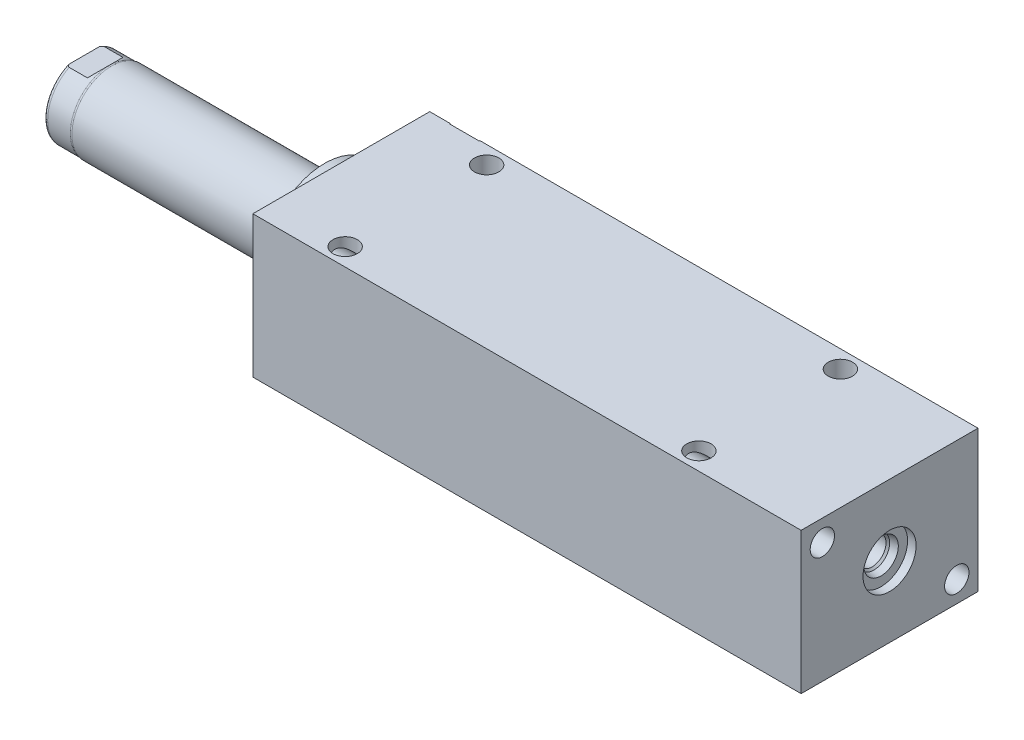
SolidWorks part; units mm, degrees
material "Alloy Steel"
ref_plane "Front Plane" through (0, 0, 0) normal (0, 0, 1) x (1, 0, 0)
ref_plane "Top Plane" through (0, 0, 0) normal (0, 1, 0) x (1, 0, 0)
ref_plane "Right Plane" through (0, 0, 0) normal (1, 0, 0) x (0, 0, -1)
ref_plane "Plane1" through (0, 0, 0) normal (1, 0, 0) x (0, 0, -1)
sketch "Sketch1" plane through (0, 0, 0) normal (1, 0, 0) x (0, 0, -1)
  line L0 (-31.75, 25.4) -> (31.75, 25.4)
  line L1 (31.75, 25.4) -> (31.75, -25.4)
  line L2 (31.75, -25.4) -> (-31.75, -25.4)
  line L3 (-31.75, -25.4) -> (-31.75, 25.4)
  line L4 (0, -24.4475) -> (0, 24.4475) construction
  dimension "D1" = 50.8
  dimension "D2" = 25.4
  dimension "D3" = 63.5
extrude "Extrude1" add sketch "Sketch1" along normal blind 196.85
ref_plane "Plane12" through (0, 17.4752, 0) normal (0, 1, 0) x (-1, 0, 0)
sketch "S2D0002" plane through (0, 17.4752, 0) normal (0, 1, 0) x (-1, 0, 0)
  line L0 (-18.8849, -31.496) -> (-22.225, -31.496)
  line L1 (-18.8849, -31.496) -> (-18.3423, -28.9433)
  line L2 (-18.3423, -28.9433) -> (-17.6784, -28.2794)
  line L3 (-17.6784, -28.2794) -> (-17.6784, -17.526)
  line L4 (-17.6784, -17.526) -> (-12.7, -17.526)
  line L5 (-12.7, -17.526) -> (-12.7, -31.75)
  line L6 (-12.7, -19.1384) -> (-12.7, 0.6985) construction
  line L7 (0, -31.75) -> (0, 31.75) construction
  line L8 (-22.225, -31.75) -> (-22.225, -31.496)
  line L9 (-196.85, -31.75) -> (0, -31.75) construction
  line L10 (-22.225, -31.75) -> (-12.7, -31.75)
  dimension "D1" = 14.224
  dimension "D2" = 12.7
  dimension "D3" = 9.9568
  dimension "D4" = 45
  dimension "D5" = 12.3698
  dimension "D6" = 12
  dimension "D7" = 2.5527
  dimension "D8" = 0.254
  dimension "D9" = 19.05
revolve "Cut-Revolve1" cut sketch "S2D0002" angle 360 about L6
ref_plane "Plane3" through (41.148, 0, -25.146) normal (0, 1, 0) x (1, 0, 0)
sketch "Sketch3" plane through (41.148, 0, -25.146) normal (0, 1, 0) x (1, 0, 0)
  line L0 (146.7993, 6.35) -> (150.1394, 6.35)
  line L1 (146.7993, 6.35) -> (146.2567, 3.7973)
  line L2 (146.2567, 3.7973) -> (145.5928, 3.1334)
  line L3 (145.5928, 3.1334) -> (145.5928, -7.62)
  line L4 (145.5928, -7.62) -> (140.6144, -7.62)
  line L5 (140.6144, -7.62) -> (140.6144, 6.604)
  line L6 (140.6144, -21.9564) -> (140.6144, 0.6985) construction
  line L7 (-41.148, 6.604) -> (-41.148, -56.896) construction
  line L8 (150.1394, 6.604) -> (150.1394, 6.35)
  line L9 (155.702, 6.604) -> (-23.1638, 6.604) construction
  line L10 (150.1394, 6.604) -> (140.6144, 6.604)
  dimension "D1" = 14.224
  dimension "D2" = 181.7624
  dimension "D3" = 9.9568
  dimension "D4" = 45
  dimension "D5" = 12
  dimension "D6" = 12.3698
  dimension "D7" = 2.5527
  dimension "D8" = 0.254
  dimension "D9" = 19.05
revolve "Cut-Revolve2" cut sketch "Sketch3" angle 360 about L6
ref_plane "Plane4" through (53.975, 0, 0) normal (0, 0, 1) x (0, -1, 0)
sketch "Sketch4" plane through (53.975, 0, 0) normal (0, 0, 1) x (0, -1, 0)
  line L0 (6.1849, 139.827) -> (9.525, 139.827)
  line L1 (6.1849, 139.827) -> (5.6423, 137.2743)
  line L2 (5.6423, 137.2743) -> (4.9784, 136.6104)
  line L3 (4.9784, 136.6104) -> (4.9784, 128.4732)
  line L4 (4.9784, 128.4732) -> (0, 128.4732)
  line L5 (0, 128.4732) -> (0, 142.875)
  line L6 (0, -15.0954) -> (0, 0.5677) construction
  line L7 (0, 142.875) -> (9.525, 142.875)
  line L9 (-25.4, 142.875) -> (25.4, 142.875) construction
  line L10 (9.525, 142.875) -> (9.525, 139.827)
  dimension "D1" = 11.3538
  dimension "D2" = 9.9568
  dimension "D3" = 3.048
  dimension "D4" = 19.05
  dimension "D5" = 2.5527
  dimension "D6" = 12
  dimension "D7" = 45
  dimension "D8" = 12.3698
revolve "Cut-Revolve3" cut sketch "Sketch4" angle 360 about L6
sketch "Sketch5" plane through (0, 0, 0) normal (-1, 0, 0) x (0, 0, 1)
  circle A0 centre (0, 0) radius 22.225
  dimension "D1" = 44.45
extrude "Extrude2" add sketch "Sketch5" along normal blind 5.969
ref_plane "Plane5" through (0, 0, 0) normal (0, -1, 0) x (0, 0, 1)
sketch "Sketch6" plane through (0, 0, 0) normal (0, -1, 0) x (0, 0, 1)
  line L0 (0, 5.969) -> (-14.2875, 5.969)
  line L1 (-14.2875, 5.969) -> (-14.2875, 92.329)
  line L2 (-14.2875, 92.329) -> (0, 92.329)
  line L3 (0, 92.329) -> (0, 5.969)
  line L4 (0, -5.7546) -> (0, 21.1709) construction
  line L5 (22.225, 5.969) -> (-22.225, 5.969) construction
  line L6 (31.75, -196.85) -> (-31.75, -196.85) construction
  dimension "D1" = 289.179
  dimension "D2" = 28.575
revolve "Revolve1" add sketch "Sketch6" angle 360 about L4
ref_plane "Plane6" through (-18.5113, 3.2639, 0) normal (0, 0, 1) x (0, 1, 0)
sketch "S2D0001" plane through (-18.5113, 3.2639, 0) normal (0, 0, 1) x (0, 1, 0)
  line L0 (2.286, 71.75) -> (2.286, 57.4347)
  line L1 (2.286, 57.4347) -> (-3.2639, 57.4347)
  line L2 (3.4798, 73.8177) -> (-3.2639, 73.8177)
  line L3 (-3.2639, 73.8177) -> (-3.2639, 57.4347)
  line L4 (2.286, 71.75) -> (3.4798, 73.8177)
  line L5 (-3.2639, -18.5113) -> (-3.2639, 2.765) construction
  line L6 (11.0236, 73.8177) -> (-17.5514, 73.8177) construction
  dimension "D1" = 30
  dimension "D2" = 13.4874
  dimension "D3" = 11.0998
  dimension "D4" = 16.383
revolve "Cut-Revolve4" cut sketch "S2D0001" angle 360 about L5
ref_plane "Plane7" through (0, 0, 0) normal (0, 1, 0) x (0, 0, -1)
sketch "Sketch8" plane through (0, 0, 0) normal (0, 1, 0) x (0, 0, -1)
  line L0 (-14.2875, 82.423) -> (-14.097, 83.185)
  line L1 (-14.097, 83.185) -> (-14.097, 91.313)
  line L2 (0, 12.6594) -> (0, 20.8178) construction
  line L3 (-14.2875, 82.423) -> (-14.2875, 92.329)
  line L4 (-13.7089, 92.329) -> (-14.2875, 92.329)
  line L5 (14.2875, 92.329) -> (-14.2875, 92.329) construction
  line L6 (-14.2875, 92.329) -> (-14.2875, 5.969) construction
  arc A0 (-13.7089, 92.329) -> (-14.097, 91.313) centre (-12.573, 91.313) ccw
  dimension "D2" = 1.524
  dimension "D1" = 28.194
  dimension "D3" = 1.016
  dimension "D4" = 0.762
  dimension "D5" = 9.144
revolve "Cut-Revolve5" cut sketch "Sketch8" angle 360 about L2
ref_plane "Plane11" through (0, 0, 0) normal (0, 0, -1) x (0, -1, 0)
sketch "Sketch12" plane through (0, 0, 0) normal (0, 0, -1) x (0, -1, 0)
  line L0 (12.573, 92.329) -> (12.573, 84.7598)
  line L1 (12.573, 84.7598) -> (14.097, 83.2358)
  line L2 (-12.573, 92.329) -> (-12.573, 84.7598)
  line L3 (-12.573, 84.7598) -> (-14.097, 83.2358)
  line L4 (12.573, 92.329) -> (14.097, 92.329)
  line L5 (0, 13.7262) -> (0, 20.767) construction
  line L6 (-14.097, 83.2358) -> (-14.097, 92.329)
  line L7 (13.7089, 92.329) -> (-13.7089, 92.329) construction
  line L8 (14.097, 83.185) -> (14.097, 91.313) construction
  line L9 (14.097, 83.2358) -> (14.097, 92.329)
  line L10 (-12.573, 92.329) -> (-14.097, 92.329)
  dimension "D1" = 25.146
  dimension "D2" = 7.5692
  dimension "D3" = 45
extrude "Cut-Extrude4" cut sketch "Sketch12" against normal mid plane 60.96
hole_wizard "Hole1" positions "Sketch15" profile "Sketch14" legacy end condition up to next
sketch "Sketch15" plane through (0, 0, 0) normal (-1, 0, 0) x (0, 0, 1)
  line L0 (0, 0) -> (-29.9914, 0) construction
  line L1 (0, 0) -> (0, 25.7648) construction
  point P0 (-24.13, -17.78)
  point P11 (24.13, 17.78)
  dimension "D1" = 17.78
  dimension "D2" = 24.13
  dimension "D3" = 35.56
  dimension "D4" = 48.26
sketch "Sketch14" plane through (0, -17.78, -24.13) normal (0, 1, 0) x (0, 0, 1)
  line L0 (0, 0) -> (0, 196.85)
  line L1 (0, 196.85) -> (4.3688, 196.85)
  line L2 (4.3688, 196.85) -> (4.3688, 0)
  line L3 (4.3688, 0) -> (0, 0)
  line L4 (0, 110) -> (0, -10) construction
  dimension "Diameter" = 8.7376
  dimension "Depth" = 196.85
hole_wizard "Hole2" positions "Sketch17" profile "Sketch16" legacy
sketch "Sketch17" plane through (0, 25.4, 0) normal (0, 1, 0) x (-1, 0, 0)
  line L0 (0, 0) -> (-59.3363, 0) construction
  line L1 (0, -31.75) -> (0, 31.75) construction
  point P0 (-26.797, -25.4)
  point P9 (-26.797, 25.4)
  dimension "D1" = 50.8
  dimension "D2" = 26.797
sketch "Sketch16" plane through (26.797, 25.4, -25.4) normal (1, 0, 0) x (0, 0, 1)
  line L0 (0, 0) -> (0, 50.8)
  line L1 (0, 50.8) -> (4.3688, 50.8)
  line L2 (4.3688, 50.8) -> (4.3688, 0)
  line L3 (4.3688, 0) -> (0, 0)
  line L4 (0, 110) -> (0, -10) construction
  dimension "Diameter" = 8.7376
  dimension "Depth" = 50.8
pattern_linear "LPattern1" count 2 spacing 127 along (1, 0, 0) of "Hole2"
